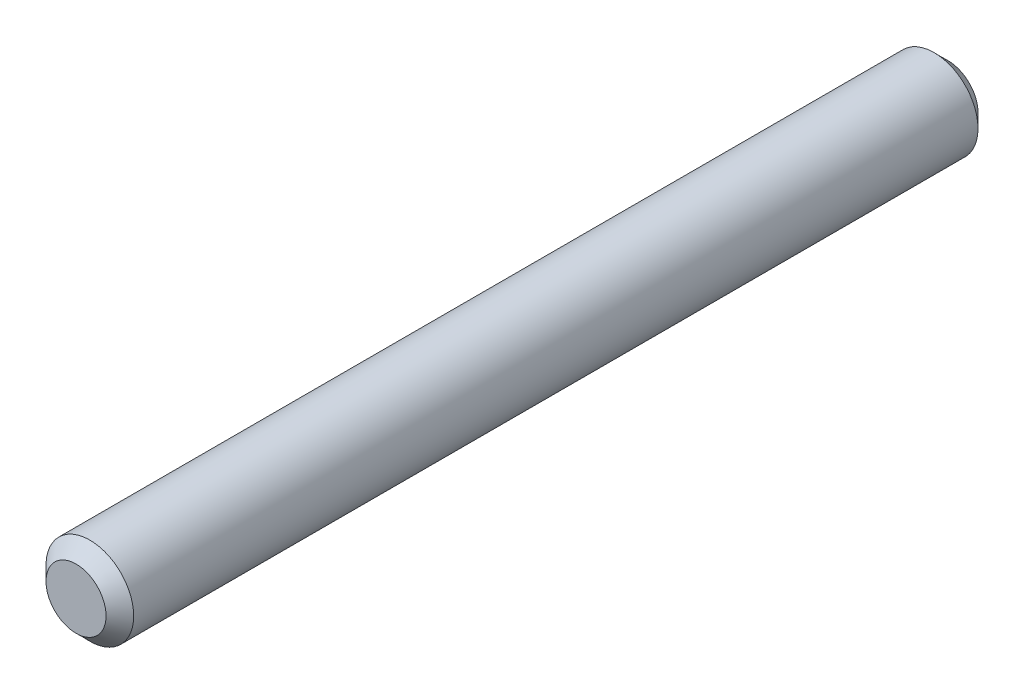
SolidWorks part; units mm, degrees
material "AISI 1020"
ref_plane "Front Plane" through (0, 0, 0) normal (0, 0, 1) x (1, 0, 0)
ref_plane "Top Plane" through (0, 0, 0) normal (0, 1, 0) x (1, 0, 0)
ref_plane "Right Plane" through (0, 0, 0) normal (1, 0, 0) x (0, 0, -1)
sketch "Sketch1" plane through (0, 0, 0) normal (0, 0, 1) x (1, 0, 0)
  circle A0 centre (0, 0) radius 3.175
  dimension "D1" = 6.35
extrude "Boss-Extrude1" add sketch "Sketch1" against normal blind 63.142
cosmetic thread "Cosmetic Thread1" parameters "D2"=5.268
chamfer "Chamfer1" distance 1 angle 45 2 edges at (3.175, 0, -63.142) (3.175, 0, 0)
